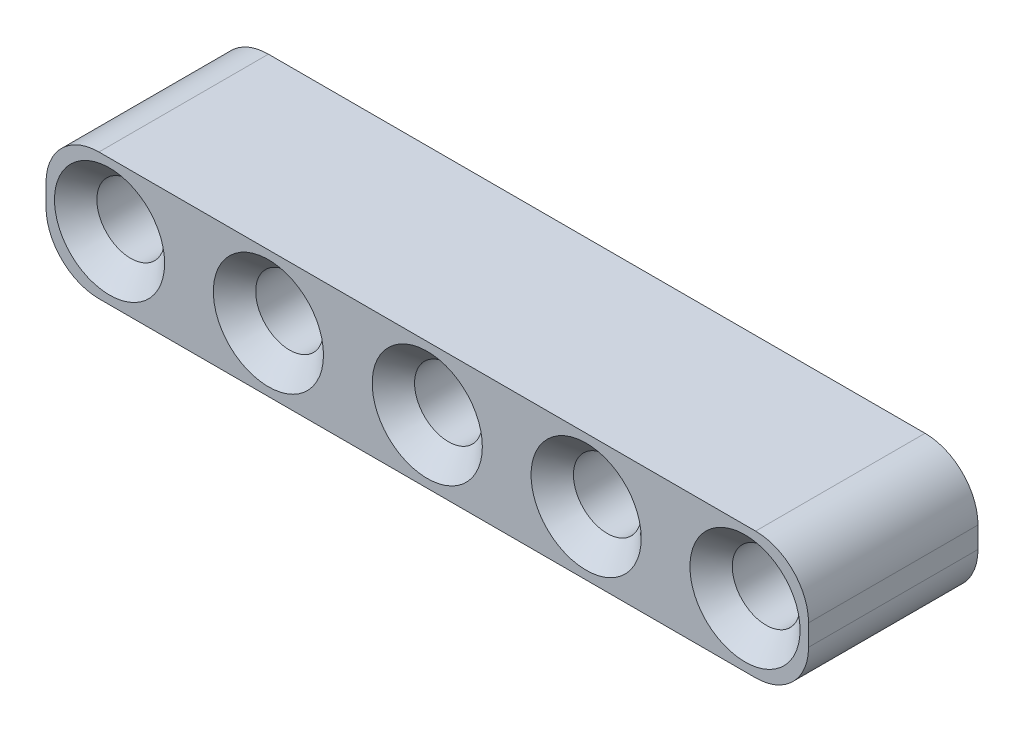
SolidWorks part; units mm, degrees
ref_plane "Front Plane" through (0, 0, 0) normal (0, 0, 1) x (1, 0, 0)
ref_plane "Top Plane" through (0, 0, 0) normal (0, 1, 0) x (1, 0, 0)
ref_plane "Right Plane" through (0, 0, 0) normal (1, 0, 0) x (0, 0, -1)
sketch "Sketch1" plane through (0, 0, 0) normal (0, 0, 1) x (1, 0, 0)
  line L1 (-0.5, 3) -> (30.5, 3)
  line L2 (-3, 0.5) -> (-3, -0.5)
  line L3 (-0.5, -3) -> (30.5, -3)
  line L4 (33, 0.5) -> (33, -0.5)
  circle A0 centre (0, 0) radius 1.6
  arc A1 (30.5, -3) -> (33, -0.5) centre (30.5, -0.5) ccw
  arc A2 (30.5, 3) -> (33, 0.5) centre (30.5, 0.5) cw
  arc A3 (-3, -0.5) -> (-0.5, -3) centre (-0.5, -0.5) ccw
  arc A4 (-0.5, 3) -> (-3, 0.5) centre (-0.5, 0.5) ccw
  circle A5 centre (7.5, 0) radius 1.6
  circle A6 centre (15, 0) radius 1.6
  circle A7 centre (22.5, 0) radius 1.6
  circle A8 centre (30, 0) radius 1.6
  point P8 (-3, 0)
  point P14 (-3, -3)
  point P17 (-3, 3)
  dimension "D1" = 3.2
  dimension "D4" = 2.5
  dimension "D2" = 6
  dimension "D3" = 3
  dimension "D6" = 7.5
  dimension "D5" = 5
extrude "Boss-Extrude1" add sketch "Sketch1" along normal blind 8
chamfer "Chamfer1" distance 1 angle 45 10 edges at (31.6, 0, 0) (31.6, 0, 8) (24.1, 0, 0) (24.1, 0, 8) (16.6, 0, 0) (16.6, 0, 8) (9.1, 0, 0) (9.1, 0, 8) (1.6, 0, 0) (1.6, 0, 8)
